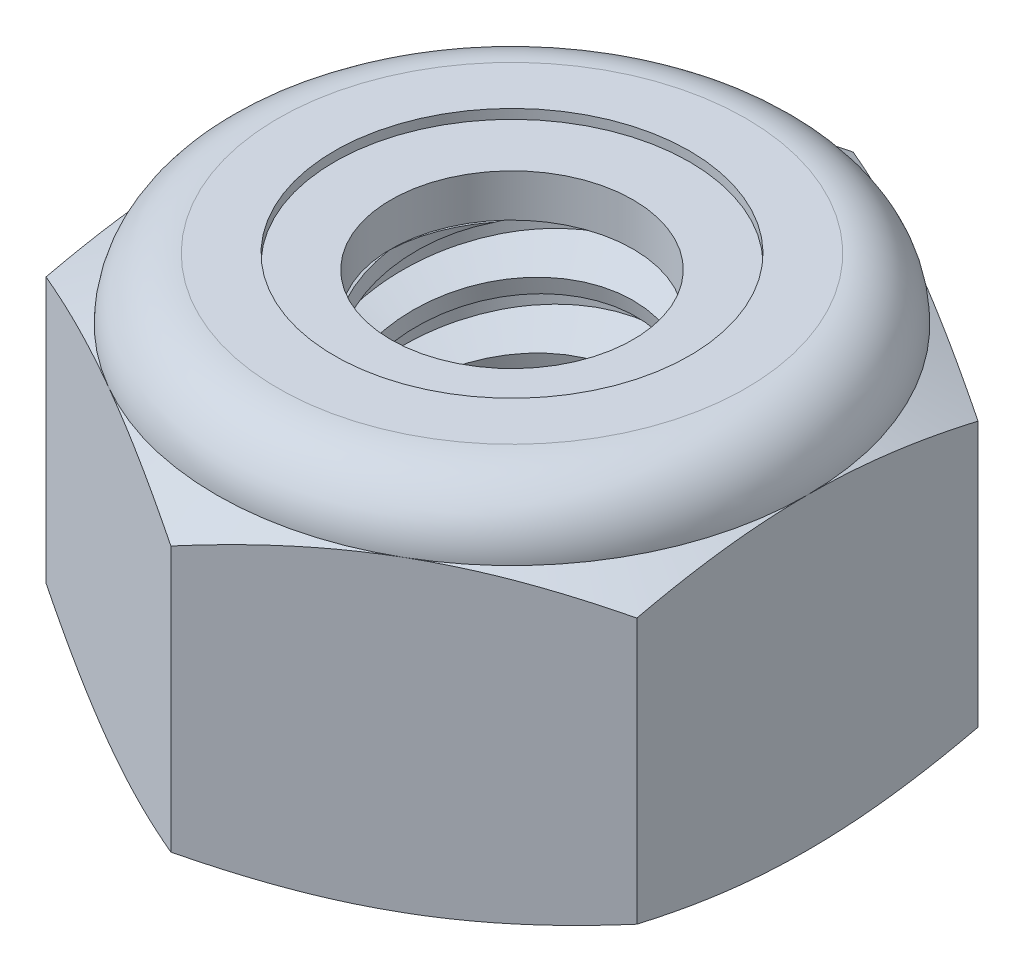
SolidWorks part; units mm, degrees
ref_plane "Front" through (0, 0, 0) normal (0, 0, 1) x (1, 0, 0)
ref_plane "Top" through (0, 0, 0) normal (0, 1, 0) x (1, 0, 0)
ref_plane "Right" through (0, 0, 0) normal (1, 0, 0) x (0, 0, -1)
sketch "Sketch1" plane through (0, 0, 0) normal (0, 1, 0) x (1, 0, 0)
  line L1 (0, 5.4993) -> (-4.7625, 2.7496)
  line L2 (-4.7625, 2.7496) -> (-4.7625, -2.7496)
  line L3 (-4.7625, -2.7496) -> (0, -5.4993)
  line L4 (0, -5.4993) -> (4.7625, -2.7496)
  line L5 (4.7625, -2.7496) -> (4.7625, 2.7496)
  line L6 (4.7625, 2.7496) -> (0, 5.4993)
  circle A0 centre (0, 0) radius 4.7625 construction
  dimension "Hex Flats" = 9.525
extrude "Extrude1" add sketch "Sketch1" along normal blind 5.9531
sketch "Sketch2" plane through (0, 0, 0) normal (1, 0, 0) x (0, 0, -1)
  line L0 (-2.413, 0) -> (-2.413, 5.9531) construction
  line L1 (0, 0) -> (2.413, 0)
  line L2 (0, 0) -> (0, 5.9531)
  line L3 (0, 5.9531) -> (2.413, 5.9531)
  line L4 (2.413, 0) -> (2.413, 5.9531)
  line L5 (-2.7496, 5.9531) -> (2.7496, 5.9531) construction
  line L7 (0, -2.413) -> (0, 0) construction
  dimension "Thread Dia" = 4.826
revolve "Revolve1" add sketch "Sketch2" angle 360 about L7
sketch "Sketch3" plane through (0, 0, 0) normal (1, 0, 0) x (0, 0, -1)
  line L0 (2.413, 5.9531) -> (-2.413, 5.9531) construction
  line L1 (-2.413, 5.9531) -> (-2.413, 4.8948) construction
  line L2 (-2.413, 4.8948) -> (2.413, 5.9531) construction
  line L3 (2.413, 5.9531) -> (2.4413, 5.8239) construction
  line L4 (2.4413, 5.8239) -> (2.6397, 4.9194)
  line L5 (2.6397, 4.9194) -> (2.0093, 5.1197)
  line L6 (2.0093, 5.1197) -> (1.9526, 5.3781)
  line L7 (1.9526, 5.3781) -> (2.4413, 5.8239)
  line L8 (1.981, 5.2489) -> (2.5405, 5.3716) construction
  line L9 (2.413, 5.9531) -> (2.413, 5.3437) construction
  line L10 (2.413, 5.3437) -> (-2.413, 4.2853) construction
  line L11 (-2.413, 4.2853) -> (-2.413, 4.8948) construction
  line L12 (-0.2497, 5.9531) -> (0.2497, 3.6759) construction
  line L13 (-2.413, 0) -> (-2.413, 5.9531) construction
  line L14 (0, 5.9531) -> (2.413, 5.9531) construction
  line L15 (2.413, 0) -> (2.413, 5.9531) construction
  point P13 (0, 4.8145)
  dimension "D1" = 0.1323
  dimension "D2" = 0.2646
  dimension "Thread Pitch" = 1.0583
  dimension "D4" = 60
  dimension "D5" = 1.0583
revolve "Cut-Revolve1" cut sketch "Sketch3" angle 360 about L12
pattern_linear "LPattern1" count 6 spacing 1.0583 along (0, -1, 0) count 2 spacing 1.0583 along (0, 1, 0) of "Cut-Revolve1"
sketch "Sketch4" plane through (0, 0, 0) normal (1, 0, 0) x (0, 0, -1)
  line L0 (0, 5.9531) -> (2.413, 5.9531)
  line L1 (2.413, 5.9531) -> (1.9526, 5.7385)
  line L2 (1.9526, 5.7385) -> (1.9526, 0.2147)
  line L3 (1.9526, 0.2147) -> (2.413, 0)
  line L4 (2.413, 0) -> (0, 0)
  line L5 (0, 0) -> (0, 5.9531)
  line L6 (2.413, 0) -> (2.413, 5.9531) construction
  line L7 (0, 5.9531) -> (2.413, 5.9531) construction
  line L8 (0, 0) -> (2.413, 0) construction
  line L9 (0, 0) -> (0, 5.9531) construction
  line L10 (0, 5.9531) -> (0, 6.4611) construction
  dimension "D1" = 25
revolve "Cut-Revolve2" cut sketch "Sketch4" angle 360 about L10
combine bodies "Combine1" operation type subtract main body 112 bodies to subtract 111
sketch "Sketch5" plane through (0, 0, 0) normal (1, 0, 0) x (0, 0, -1)
  line L0 (0, 0) -> (4.7625, 0)
  line L1 (4.7625, 0) -> (5.4993, 0.3436)
  line L2 (5.4993, 0.3436) -> (5.4993, 4.6174)
  line L3 (5.4993, 4.6174) -> (4.7625, 4.9609)
  line L4 (3.7703, 5.9531) -> (3.7703, 7.2231)
  line L5 (3.7703, 7.2231) -> (6.7693, 7.2231)
  line L6 (6.7693, 7.2231) -> (6.7693, -1.27)
  line L7 (6.7693, -1.27) -> (0, -1.27)
  line L8 (0, -1.27) -> (0, 0)
  line L9 (4.7625, 4.9609) -> (4.7625, 0) construction
  line L10 (0, 0) -> (2.413, 0) construction
  line L13 (5.4993, 2.4805) -> (6.7693, 2.4805) construction
  line L14 (5.4993, 5.9531) -> (5.4993, 0) construction
  line L15 (0, 0) -> (0, 7.2231) construction
  line L20 (0, 7.2231) -> (3.7703, 7.2231) construction
  line L22 (0, 5.9531) -> (2.413, 5.9531) construction
  arc A0 (4.7625, 4.9609) -> (3.7703, 5.9531) centre (3.7703, 4.9609) ccw
  dimension "D1" = 25
  dimension "D2" = 1.27
  dimension "D3" = 5.9531
  dimension "D4" = 0.9922
revolve "Cut-Revolve3" cut sketch "Sketch5" angle 360 about L15
sketch "Sketch6" plane through (0, 0, 0) normal (1, 0, 0) x (0, 0, -1)
  line L0 (0, 4.9609) -> (4.6101, 4.9609)
  line L1 (3.7703, 5.8007) -> (2.8615, 5.8007)
  line L2 (0, 7.2231) -> (0, 4.9609)
  line L3 (2.8615, 7.2231) -> (0, 7.2231)
  line L4 (0, 7.2231) -> (3.7703, 7.2231) construction
  line L5 (0, 0) -> (0, 7.2231) construction
  line L6 (0, 7.2231) -> (0, 44.323) construction
  line L7 (2.8615, 5.8007) -> (2.8615, 7.2231)
  line L8 (3.7703, 5.9531) -> (3.7703, 5.8007) construction
  line L9 (2.8615, 5.8007) -> (1.9526, 5.8007) construction
  line L10 (1.9526, 5.8007) -> (1.9526, 5.7385) construction
  arc A0 (4.6101, 4.9609) -> (3.7703, 5.8007) centre (3.7703, 4.9609) ccw
  arc A1 (4.7625, 4.9609) -> (3.7703, 5.9531) centre (3.7703, 4.9609) ccw construction
  dimension "D1" = 0.1524
revolve "Cut-Revolve4" cut sketch "Sketch6" angle 360 about L6
sketch "Sketch7" plane through (0, 0, 0) normal (1, 0, 0) x (0, 0, -1)
  line L0 (1.9526, 5.0371) -> (4.5301, 5.0371)
  line L1 (3.7703, 5.7245) -> (1.9526, 5.7245)
  line L2 (1.9526, 5.7245) -> (1.9526, 5.0371)
  line L3 (1.9526, 5.0371) -> (0, 5.0371) construction
  line L4 (0, 5.0371) -> (0, 5.7245) construction
  line L5 (0, 5.7245) -> (1.9526, 5.7245) construction
  line L6 (1.9526, 5.0371) -> (1.9526, 4.9609) construction
  line L7 (0, 4.9609) -> (4.6101, 4.9609) construction
  line L8 (3.7703, 5.7245) -> (3.7703, 5.8007) construction
  arc A0 (4.5301, 5.0371) -> (3.7703, 5.7245) centre (3.7703, 4.9609) ccw
  arc A2 (4.6101, 4.9609) -> (3.7703, 5.8007) centre (3.7703, 4.9609) ccw construction
  dimension "D1" = 0.0762
revolve "Revolve2" add sketch "Sketch7" angle 360 about L4
equation "\"D1@Sketch3\"=\"Thread Pitch@Sketch3\"/8"
equation "\"D2@Sketch3\"=\"Thread Pitch@Sketch3\"/4"
equation "\"D5@Sketch3\"=\"Thread Pitch@Sketch3\""
equation "\"D4@LPattern1\"=\"Thread Pitch@Sketch3\""
equation "\"D3@LPattern1\"=\"Thread Pitch@Sketch3\""
equation "\"D1@LPattern1\"=\"Height@Extrude1\"/\"Thread Pitch@Sketch3\""
equation "\"D4@Sketch5\"=\"Height@Extrude1\"/6"
